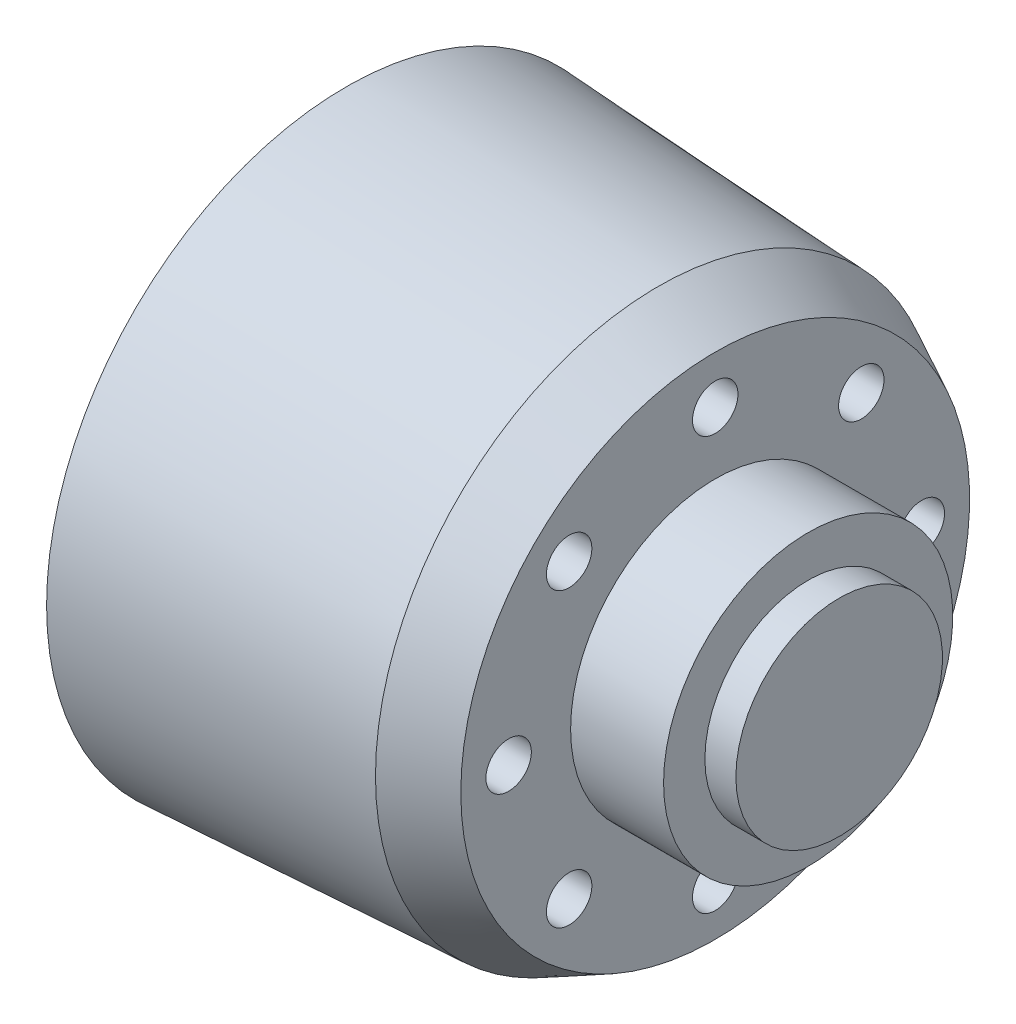
SolidWorks part; units mm, degrees
ref_plane "Front Plane" through (0, 0, 0) normal (0, 0, 1) x (1, 0, 0)
ref_plane "Top Plane" through (0, 0, 0) normal (0, 1, 0) x (1, 0, 0)
ref_plane "Right Plane" through (0, 0, 0) normal (1, 0, 0) x (0, 0, -1)
sketch "Sketch1" plane through (0, 0, 0) normal (0, 1, 0) x (1, 0, 0)
  line L0 (-18.2338, 0) -> (23.1429, 0) construction
  line L2 (10.1939, 12.315) -> (10.1939, 7)
  line L5 (-7.673, 0) -> (-7.673, 14.5)
  line L7 (10.1939, 7) -> (14.6939, 7)
  line L8 (14.6939, 7) -> (14.6939, 5)
  line L10 (14.6939, 5) -> (16.1939, 5)
  line L11 (16.1939, 5) -> (16.1939, 0)
  line L12 (-7.673, 0) -> (16.1939, 0)
  line L13 (-7.673, 14.5) -> (7.4378, 13.69)
  line L14 (7.4378, 13.69) -> (10.1939, 12.315)
  dimension "D1" = 24.63
  dimension "D2" = 29
  dimension "D3" = 18
  dimension "D4" = 14
  dimension "D5" = 4.5
  dimension "D6" = 1.5
  dimension "D7" = 10
  dimension "D8" = 27.38
  dimension "D9" = 3.08
  dimension "D10" = 1.375
revolve "Revolve1" add sketch "Sketch1" angle 360 about L0
sketch "Sketch2" plane through (-7.673, 0, 0) normal (-1, 0, 0) x (0, 0, 1)
  circle A0 centre (0, 0) radius 4.45
  dimension "D1" = 8.9
extrude "Cut-Extrude1" cut sketch "Sketch2" against normal offset from surface (7 mm away) 7 up to face at (-7.673, 0, 14.5)
sketch "Sketch3" plane through (10.1939, 0, 0) normal (1, 0, 0) x (0, 0, -1)
  circle A0 centre (0, 0) radius 10 construction
  circle A1 centre (0, 10) radius 1.1
  circle A2 centre (7.0711, 7.0711) radius 1.1
  circle A3 centre (10, 0) radius 1.1
  circle A4 centre (7.0711, -7.0711) radius 1.1
  circle A5 centre (0, -10) radius 1.1
  circle A6 centre (-7.0711, -7.0711) radius 1.1
  circle A7 centre (-10, 0) radius 1.1
  circle A8 centre (-7.0711, 7.0711) radius 1.1
  point P22 (0, 0)
  dimension "D1" = 20
  dimension "D2" = 2.2
  dimension "D3" = 8
extrude "Cut-Extrude2" cut sketch "Sketch3" against normal through all
sketch "Sketch4" plane through (-7.673, 0, 0) normal (-1, 0, 0) x (0, 0, 1)
  circle A0 centre (0, 0) radius 10 construction
  circle A1 centre (0, 10) radius 2.5
  circle A2 centre (7.0711, 7.0711) radius 2.5
  circle A3 centre (10, 0) radius 2.5
  circle A4 centre (7.0711, -7.0711) radius 2.5
  circle A5 centre (0, -10) radius 2.5
  circle A6 centre (-7.0711, -7.0711) radius 2.5
  circle A7 centre (-10, 0) radius 2.5
  circle A8 centre (-7.0711, 7.0711) radius 2.5
  point P22 (0, 0)
  dimension "D1" = 20
  dimension "D2" = 5
  dimension "D3" = 8
extrude "Cut-Extrude3" cut sketch "Sketch4" against normal offset from surface (14.8669 mm away) 3 up to face at (10.1939, 10, -1.1)
